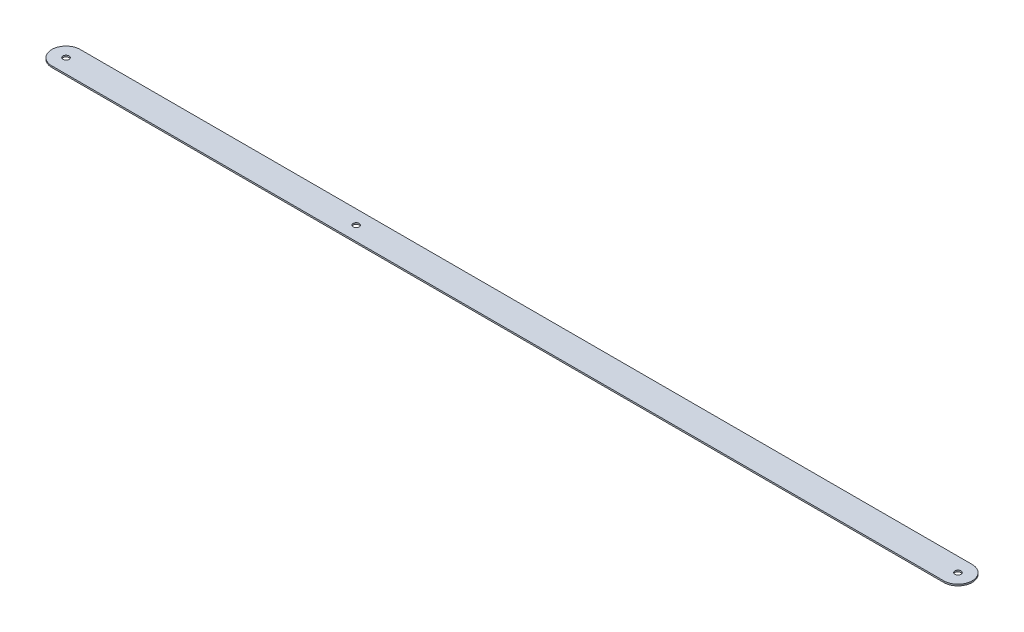
SolidWorks part; units mm, degrees
ref_plane "Front Plane" through (0, 0, 0) normal (0, 0, 1) x (1, 0, 0)
ref_plane "Top Plane" through (0, 0, 0) normal (0, 1, 0) x (1, 0, 0)
ref_plane "Right Plane" through (0, 0, 0) normal (1, 0, 0) x (0, 0, -1)
sketch "Sketch1" plane through (0, 0, 0) normal (0, 1, 0) x (1, 0, 0)
  line L0 (0, 0) -> (880.4, 0) construction
  line L1 (0, 14) -> (880.4, 14)
  line L2 (0, -14) -> (880.4, -14)
  arc A0 (0, 14) -> (0, -14) centre (0, 0) ccw
  arc A1 (880.4, -14) -> (880.4, 14) centre (880.4, 0) ccw
  circle A2 centre (880.4, 0) radius 3
  circle A3 centre (0, 0) radius 3
  circle A4 centre (286.33, 0) radius 3
  point P3 (440.2, 0)
  dimension "D2" = 14
  dimension "D3" = 6
  dimension "D4" = 594.07
  dimension "D1" = 880.4
extrude "Boss-Extrude1" add sketch "Sketch1" along normal blind 1.5
